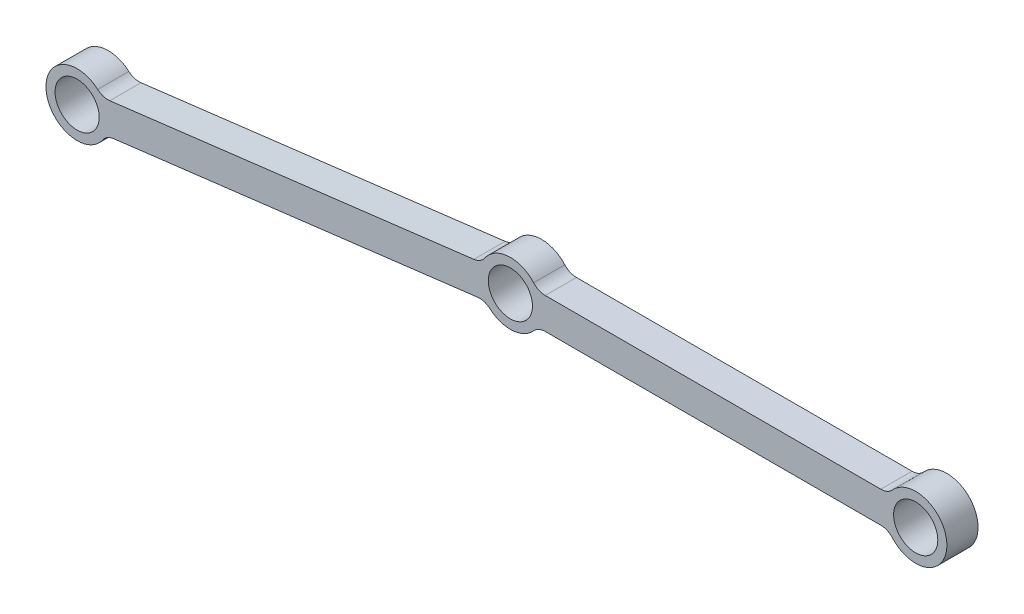
SolidWorks part; units mm, degrees
ref_plane "Front Plane" through (0, 0, 0) normal (0, 0, 1) x (1, 0, 0)
ref_plane "Top Plane" through (0, 0, 0) normal (0, 1, 0) x (1, 0, 0)
ref_plane "Right Plane" through (0, 0, 0) normal (1, 0, 0) x (0, 0, -1)
sketch "Sketch1" plane through (0, 0, 0) normal (0, 0, 1) x (1, 0, 0)
  line L0 (0, 0) -> (82.55, 0)
  line L1 (0, 0) -> (-88.2374, -10.8342)
  line L2 (-87.4635, -17.1369) -> (0.7739, -6.3027)
  line L3 (-89.0112, -4.5315) -> (-0.7739, 6.3027)
  line L4 (0, -6.35) -> (82.55, -6.35)
  line L5 (0, 6.35) -> (82.55, 6.35)
  line L6 (-83.166, -7.0127) -> (-5.8452, 2.4811)
  line L7 (5.4993, 3.175) -> (77.0507, 3.175)
  line L8 (-88.6243, -7.6829) -> (-0.3869, 3.1513) construction
  line L9 (0, 3.175) -> (82.55, 3.175) construction
  line L10 (-82.3921, -13.3153) -> (-5.0713, -3.8215)
  line L12 (5.4993, -3.175) -> (77.0507, -3.175)
  circle A0 centre (0, 0) radius 4.4996
  circle A1 centre (0, 0) radius 6.35
  circle A2 centre (-88.2374, -10.8342) radius 4.4996
  circle A3 centre (-88.2374, -10.8342) radius 6.35
  circle A5 centre (82.55, 0) radius 4.4996
  circle A6 centre (82.55, 0) radius 6.35
  dimension "D1" = 8.9992
  dimension "D2" = 12.7
  dimension "D5" = 8.9992
  dimension "D6" = 12.7
  dimension "D7" = 82.55
  dimension "D8" = 8.9992
  dimension "D9" = 12.7
  dimension "D3" = 88.9
  dimension "D4" = 173
  dimension "D10" = 3.175
  dimension "D11" = 3.175
  dimension "D12" = 3.175
extrude "Boss-Extrude2" add sketch "Sketch1" against normal blind 6.35
fillet "Fillet2" radius 3.175 8 edges at (77.0507, 3.175, -3.175) (77.0507, -3.175, -3.175) (-5.0713, -3.8215, -3.175) (-5.8452, 2.4811, -3.175) (5.4993, 3.175, -3.175) (5.4993, -3.175, -3.175) (-82.3921, -13.3153, -3.175) (-83.166, -7.0127, -3.175)
